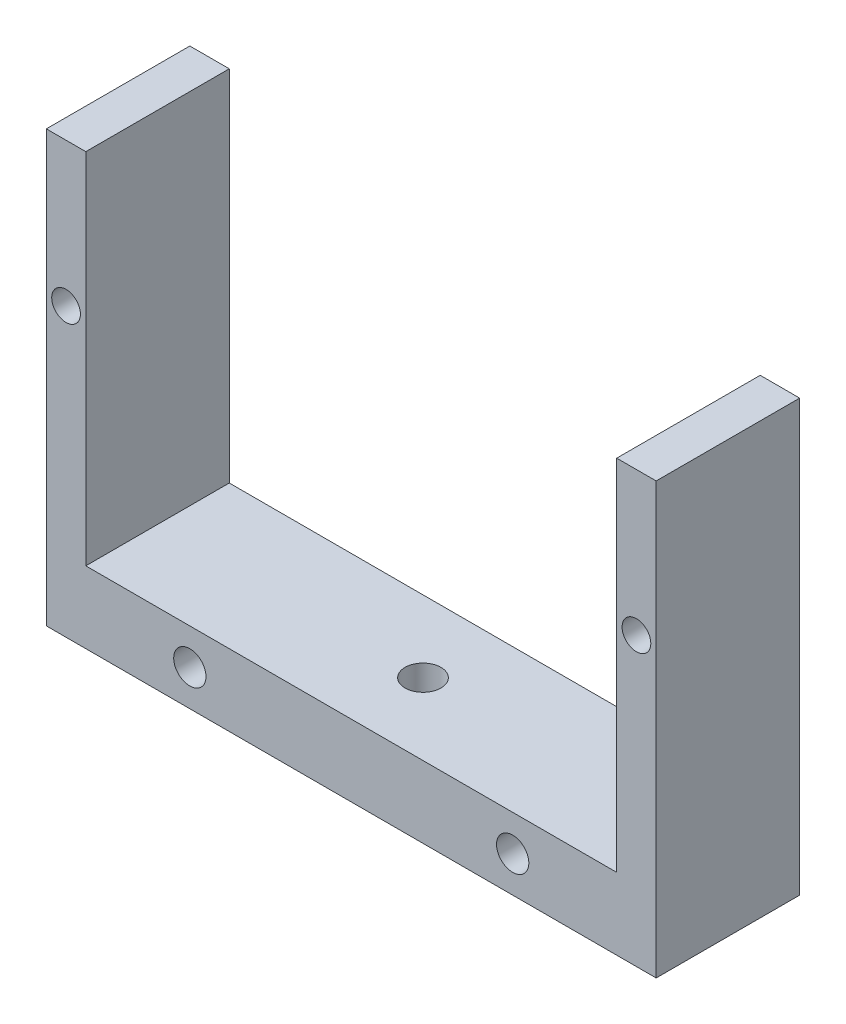
SolidWorks part; units mm, degrees
ref_plane "Front Plane" through (0, 0, 0) normal (0, 0, 1) x (1, 0, 0)
ref_plane "Top Plane" through (0, 0, 0) normal (0, 1, 0) x (1, 0, 0)
ref_plane "Right Plane" through (0, 0, 0) normal (1, 0, 0) x (0, 0, -1)
sketch "Sketch1" plane through (0, 0, 0) normal (0, 0, 1) x (1, 0, 0)
  line L0 (-58.1407, -46.1718) -> (26.8593, -46.1718)
  line L1 (26.8593, -46.1718) -> (26.8593, 13.8282)
  line L2 (26.8593, 13.8282) -> (21.3593, 13.8282)
  line L3 (21.3593, 13.8282) -> (21.3593, -36.1718)
  line L4 (21.3593, -36.1718) -> (-52.6407, -36.1718)
  line L5 (-52.6407, -36.1718) -> (-52.6407, 13.8282)
  line L6 (-52.6407, 13.8282) -> (-58.1407, 13.8282)
  line L7 (-58.1407, 13.8282) -> (-58.1407, -46.1718)
  dimension "D1" = 85
  dimension "D2" = 60
  dimension "D3" = 60
  dimension "D4" = 10
  dimension "D5" = 5.5
  dimension "D6" = 5.5
extrude "Boss-Extrude1" add sketch "Sketch1" along normal blind 20
sketch "Sketch2" plane through (0, 0, 0) normal (0, 0, -1) x (-1, 0, 0)
  line L0 (58.1407, -46.1718) -> (-26.8593, -46.1718) construction
  line L1 (58.1407, 13.8282) -> (58.1407, -46.1718) construction
  line L2 (-26.8593, -46.1718) -> (-26.8593, 13.8282) construction
  circle A0 centre (-6.8593, -41.1718) radius 2.25
  circle A1 centre (38.1407, -41.1718) radius 2.25
  dimension "D1" = 5
  dimension "D2" = 5
  dimension "D3" = 20
  dimension "D4" = 20
  dimension "D5" = 4.5
  dimension "D6" = 4.5
extrude "Cut-Extrude1" cut sketch "Sketch2" against normal blind 20
sketch "Sketch3" plane through (0, 0, 20) normal (0, 0, 1) x (1, 0, 0)
  line L0 (-58.1407, 13.8282) -> (-58.1407, -46.1718) construction
  line L1 (26.8593, -46.1718) -> (26.8593, 13.8282) construction
  line L2 (26.8593, 13.8282) -> (21.3593, 13.8282) construction
  line L3 (-52.6407, 13.8282) -> (-58.1407, 13.8282) construction
  circle A0 centre (-55.3907, -6.1718) radius 2
  circle A1 centre (24.1093, -6.1718) radius 2
  dimension "D1" = 4
  dimension "D2" = 2.75
  dimension "D3" = 2.75
  dimension "D4" = 20
  dimension "D5" = 20
  dimension "D6" = 4
extrude "Cut-Extrude2" cut sketch "Sketch3" against normal up to next
sketch "Sketch4" plane through (0, -36.1718, 0) normal (0, 1, 0) x (1, 0, 0)
  line L0 (26.8593, -20) -> (26.8593, 0) construction
  line L1 (21.3593, 0) -> (-52.6407, 0) construction
  circle A0 centre (-15.6407, -10) radius 2.5
  point P4 (-15.6407, 0)
  dimension "D1" = 42.5
  dimension "D2" = 10
  dimension "D3" = 5
extrude "Cut-Extrude3" cut sketch "Sketch4" against normal up to next
